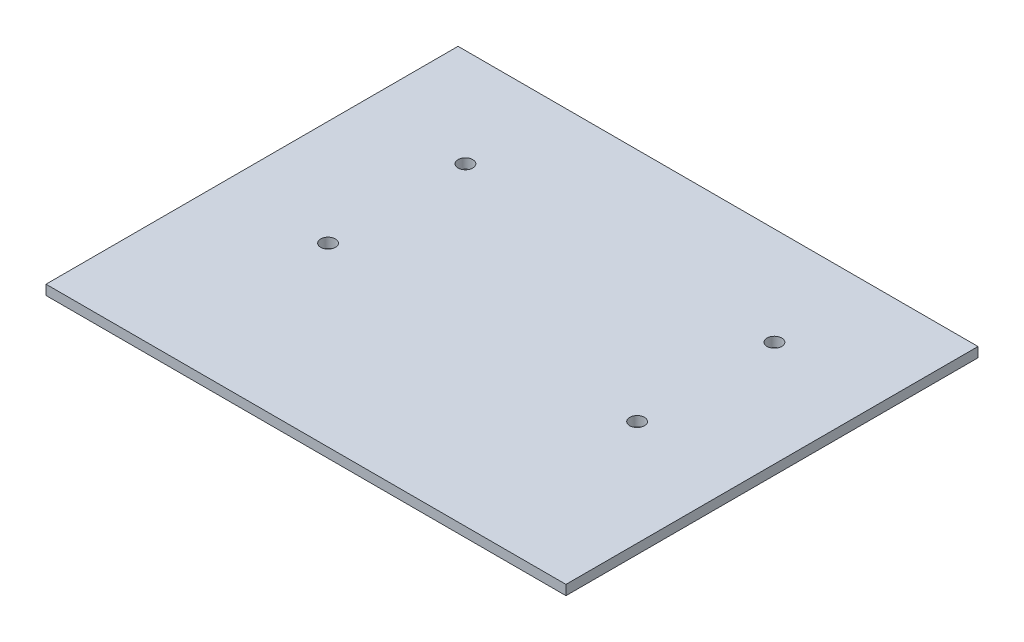
SolidWorks part; units mm, degrees
ref_plane "Front Plane" through (0, 0, 0) normal (0, 0, 1) x (1, 0, 0)
ref_plane "Top Plane" through (0, 0, 0) normal (0, 1, 0) x (1, 0, 0)
ref_plane "Right Plane" through (0, 0, 0) normal (1, 0, 0) x (0, 0, -1)
sketch "Sketch1" plane through (0, 0, 0) normal (0, 1, 0) x (1, 0, 0)
  line L1 (0, 0) -> (106, 0)
  line L2 (0, 0) -> (0, 84)
  line L3 (0, 84) -> (106, 84)
  line L4 (106, 0) -> (106, 84)
  circle A0 centre (84.5, 64) radius 1.5
  circle A1 centre (84.5, 36) radius 1.5
  circle A2 centre (21.5, 36) radius 1.5
  circle A3 centre (21.5, 64) radius 1.5
  dimension "D1" = 106
  dimension "D2" = 84
  dimension "D6" = 28
extrude "Boss-Extrude1" add sketch "Sketch1" along normal blind 2
